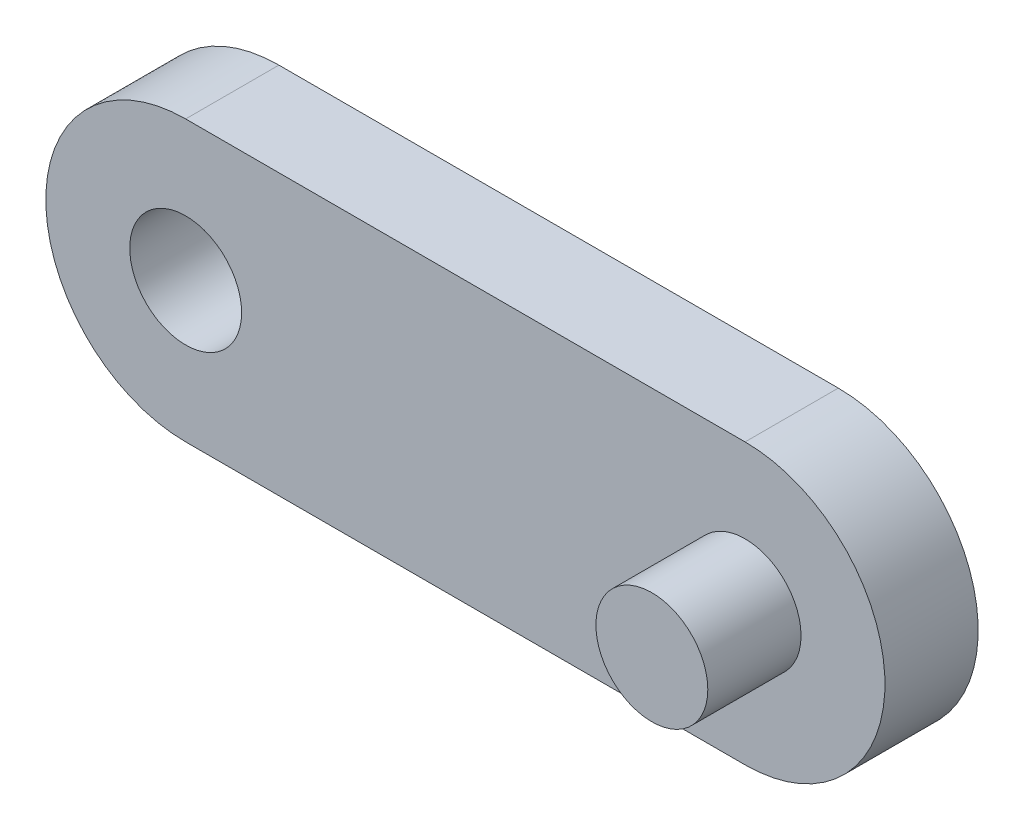
SolidWorks part; units mm, degrees
material "ABS"
ref_plane "Alzado" through (0, 0, 0) normal (0, 0, 1) x (1, 0, 0)
ref_plane "Planta" through (0, 0, 0) normal (0, 1, 0) x (1, 0, 0)
ref_plane "Vista lateral" through (0, 0, 0) normal (1, 0, 0) x (0, 0, -1)
sketch "Croquis1" plane through (0, 0, 0) normal (0, 0, 1) x (1, 0, 0)
  line L0 (0, 0) -> (60, 0) construction
  line L1 (0, 15) -> (60, 15)
  line L2 (0, -15) -> (60, -15)
  arc A0 (0, 15) -> (0, -15) centre (0, 0) ccw
  arc A1 (60, -15) -> (60, 15) centre (60, 0) ccw
  circle A2 centre (0, 0) radius 6
  point P3 (30, 0)
  dimension "D1" = 12
  dimension "D2" = 60
  dimension "D3" = 30
extrude "Saliente-Extruir1" add sketch "Croquis1" along normal blind 10
sketch "Croquis2" plane through (0, 0, 10) normal (0, 0, 1) x (1, 0, 0)
  line L0 (75, 0) -> (60, 0) construction
  arc A0 (60, -15) -> (60, 15) centre (60, 0) ccw construction
  circle A1 centre (60, 0) radius 6
  dimension "D1" = 12
extrude "Saliente-Extruir2" add sketch "Croquis2" along normal blind 10
